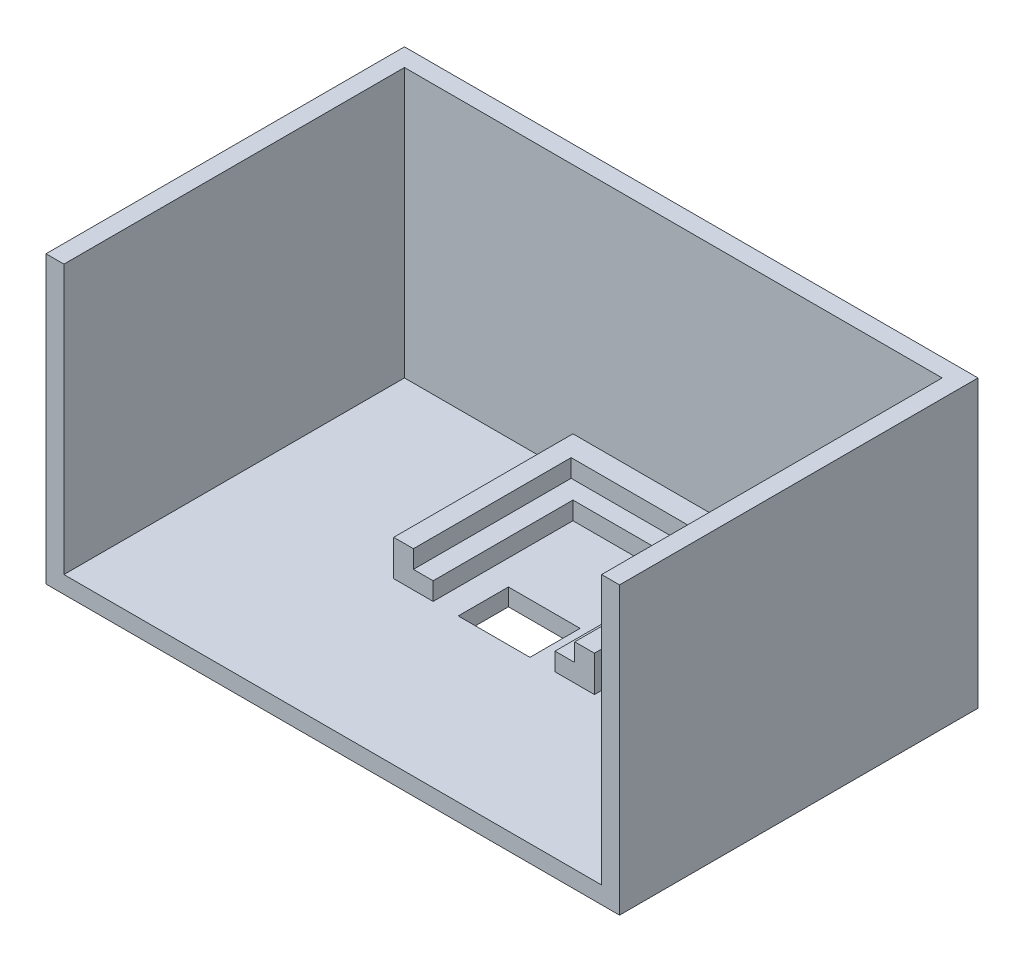
SolidWorks part; units mm, degrees
ref_plane "Front" through (0, 0, 0) normal (0, 0, 1) x (1, 0, 0)
ref_plane "Top" through (0, 0, 0) normal (0, 1, 0) x (1, 0, 0)
ref_plane "Right" through (0, 0, 0) normal (1, 0, 0) x (0, 0, -1)
sketch "Sketch1" plane through (0, 0, 0) normal (0, 1, 0) x (1, 0, 0)
  line L1 (-66.7097, 42.0726) -> (13.2903, 42.0726)
  line L2 (-66.7097, 42.0726) -> (-66.7097, -7.9274)
  line L3 (-66.7097, -7.9274) -> (13.2903, -7.9274)
  line L4 (13.2903, 42.0726) -> (13.2903, -7.9274)
  dimension "D1" = 80
  dimension "D2" = 50
extrude "Boss-Extrude1" add sketch "Sketch1" along normal blind 2.5
sketch "Sketch2" plane through (0, 2.5, 0) normal (0, 1, 0) x (1, 0, 0)
  line L1 (-66.7097, 42.0726) -> (13.2903, 42.0726)
  line L2 (-66.7097, 42.0726) -> (-66.7097, -7.9274)
  line L3 (-66.7097, -7.9274) -> (13.2903, -7.9274)
  line L4 (13.2903, 42.0726) -> (13.2903, -7.9274)
  line L5 (10.7903, -5.4274) -> (-64.2097, -5.4274)
  line L6 (10.7903, -5.4274) -> (10.7903, 39.5726)
  line L7 (10.7903, 39.5726) -> (-64.2097, 39.5726)
  line L8 (-64.2097, -5.4274) -> (-64.2097, 39.5726)
  line L9 (-26.7097, 39.5726) -> (-26.7097, -5.4274) construction
  line L10 (10.7903, 17.0726) -> (-64.2097, 17.0726) construction
  point P4 (-26.7097, 17.0726)
  dimension "D1" = 50
  dimension "D2" = 80
  dimension "D3" = 45
  dimension "D4" = 75
  dimension "D5" = 2.5
extrude "Boss-Extrude2" add sketch "Sketch2" along normal blind 37.5
sketch "Sketch5" plane through (0, 0, 7.9274) normal (0, 0, 1) x (1, 0, 0)
  line L1 (-66.7097, 0) -> (13.2903, 0) construction
  line L2 (-20.4049, 2.5) -> (-33.0144, 2.5)
  arc A0 (-33.0144, 2.5) -> (-20.4049, 2.5) centre (-26.7097, 15) cw
  dimension "D1" = 40
  dimension "D4" = 14
  dimension "D2" = 2.5
  dimension "D3" = 2.5
  dimension "D5" = 15
extrude "Cut-Extrude2" cut sketch "Sketch5" against normal blind 2.5
sketch "Sketch6" plane through (0, 2.5, 0) normal (0, 1, 0) x (1, 0, 0)
  line L1 (-40.7097, 39.5726) -> (-12.7097, 39.5726)
  line L2 (-40.7097, 39.5726) -> (-40.7097, 14.5726)
  line L3 (-35.2097, 14.5726) -> (-40.7097, 14.5726)
  line L4 (-12.7097, 39.5726) -> (-12.7097, 14.5726)
  line L5 (-12.7097, 14.5726) -> (-18.2097, 14.5726)
  line L6 (-35.2097, 34.0726) -> (-18.2097, 34.0726)
  line L7 (-35.2097, 34.0726) -> (-35.2097, 14.5726)
  line L9 (-18.2097, 34.0726) -> (-18.2097, 14.5726)
  dimension "D1" = 25
  dimension "D2" = 28
  dimension "D3" = 26
  dimension "D4" = 20
  dimension "D5" = 19.5
  dimension "D6" = 17
  dimension "D7" = 31.5
sketch "Sketch8" plane through (0, 2.5, 0) normal (0, 1, 0) x (1, 0, 0)
  line L1 (-31.7097, 14.5726) -> (-21.7097, 14.5726)
  line L2 (-31.7097, 14.5726) -> (-31.7097, 21.5726)
  line L3 (-31.7097, 21.5726) -> (-21.7097, 21.5726)
  line L4 (-21.7097, 14.5726) -> (-21.7097, 21.5726)
  dimension "D1" = 7
  dimension "D2" = 10
  dimension "D3" = 18
  dimension "D4" = 32.5
sketch "Sketch11" plane through (0, 0, 0) normal (0, -1, 0) x (-1, 0, 0)
  line L1 (66.7097, -7.9274) -> (-13.2903, -7.9274)
  line L2 (66.7097, -7.9274) -> (66.7097, 42.0726)
  line L3 (66.7097, 42.0726) -> (-13.2903, 42.0726)
  line L4 (-13.2903, -7.9274) -> (-13.2903, 42.0726)
  dimension "D1" = 50
  dimension "D2" = 80
extrude "Cut-Extrude10" cut sketch "Sketch11" against normal blind 0.1
extrude "Boss-Extrude4" add sketch "Sketch6" along normal blind 5
sketch "Sketch14" plane through (0, 7.5, 0) normal (0, 1, 0) x (1, 0, 0)
  line L1 (-37.9597, 36.5726) -> (-15.4597, 36.5726)
  line L2 (-37.9597, 36.5726) -> (-37.9597, 14.5726)
  line L3 (-37.9597, 14.5726) -> (-15.4597, 14.5726)
  line L4 (-15.4597, 36.5726) -> (-15.4597, 14.5726)
  dimension "D1" = 22
  dimension "D2" = 22.5
  dimension "D3" = 2.75
  dimension "D4" = 27.5
  dimension "D5" = 2.75
extrude "Cut-Extrude14" cut sketch "Sketch8" against normal blind 10
sketch "Sketch15" plane through (0, 0, 5.4274) normal (0, 0, -1) x (-1, 0, 0)
  line L0 (20.4049, 2.5) -> (-10.7903, 2.5) construction
  line L1 (-10.7903, 2.5) -> (64.2097, 2.5)
  line L2 (-10.7903, 2.5) -> (-10.7903, 40)
  line L3 (-10.7903, 40) -> (64.2097, 40)
  line L4 (64.2097, 2.5) -> (64.2097, 40)
extrude "Cut-Extrude15" cut sketch "Sketch15" against normal blind 10
extrude "Cut-Extrude16" cut sketch "Sketch14" against normal blind 2.5
